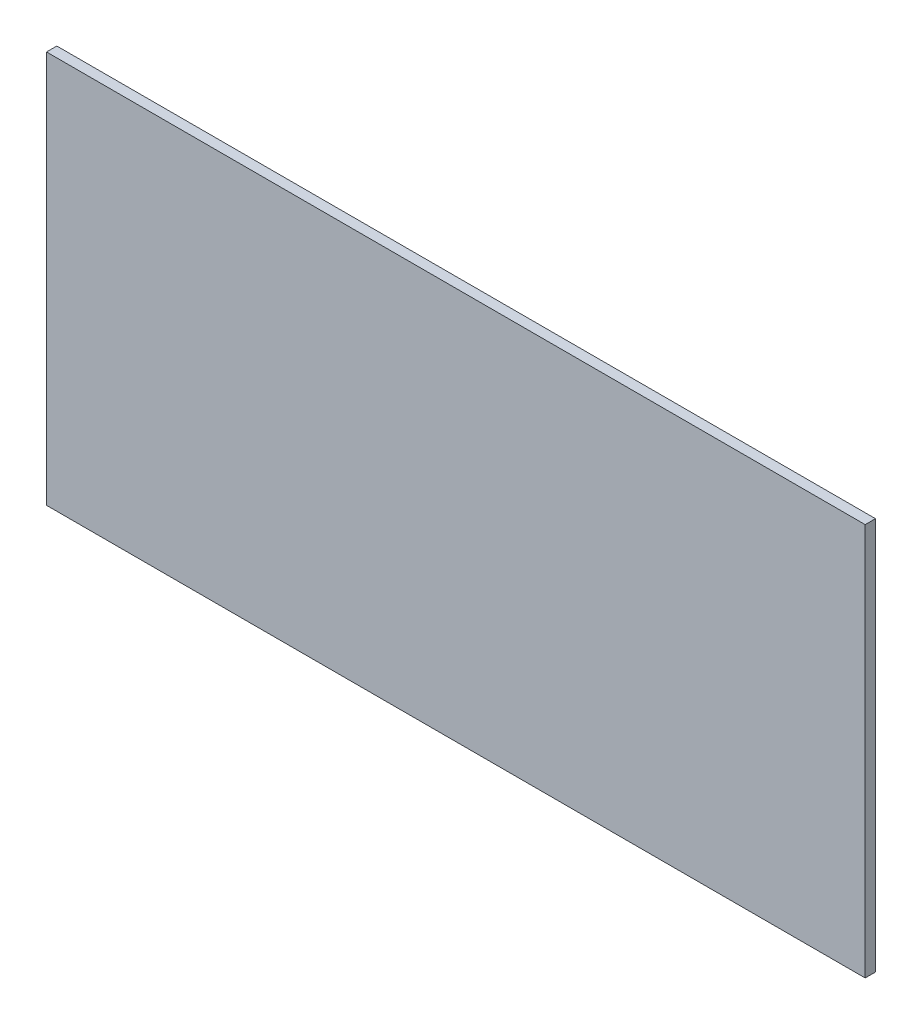
SolidWorks part; units mm, degrees
material "Pine"
ref_plane "Front Plane" through (0, 0, 0) normal (0, 0, 1) x (1, 0, 0)
ref_plane "Top Plane" through (0, 0, 0) normal (0, 1, 0) x (1, 0, 0)
ref_plane "Right Plane" through (0, 0, 0) normal (1, 0, 0) x (0, 0, -1)
sketch "Sketch1" plane through (0, 0, 0) normal (0, 0, 1) x (1, 0, 0)
  line L1 (-473.3294, 454.025) -> (473.3294, 454.025)
  line L2 (-473.3294, 454.025) -> (-473.3294, 0)
  line L3 (-473.3294, 0) -> (473.3294, 0)
  line L4 (473.3294, 454.025) -> (473.3294, 0)
extrude "Boss-Extrude1" add sketch "Sketch1" against normal up to surface (11.9063 mm away)
